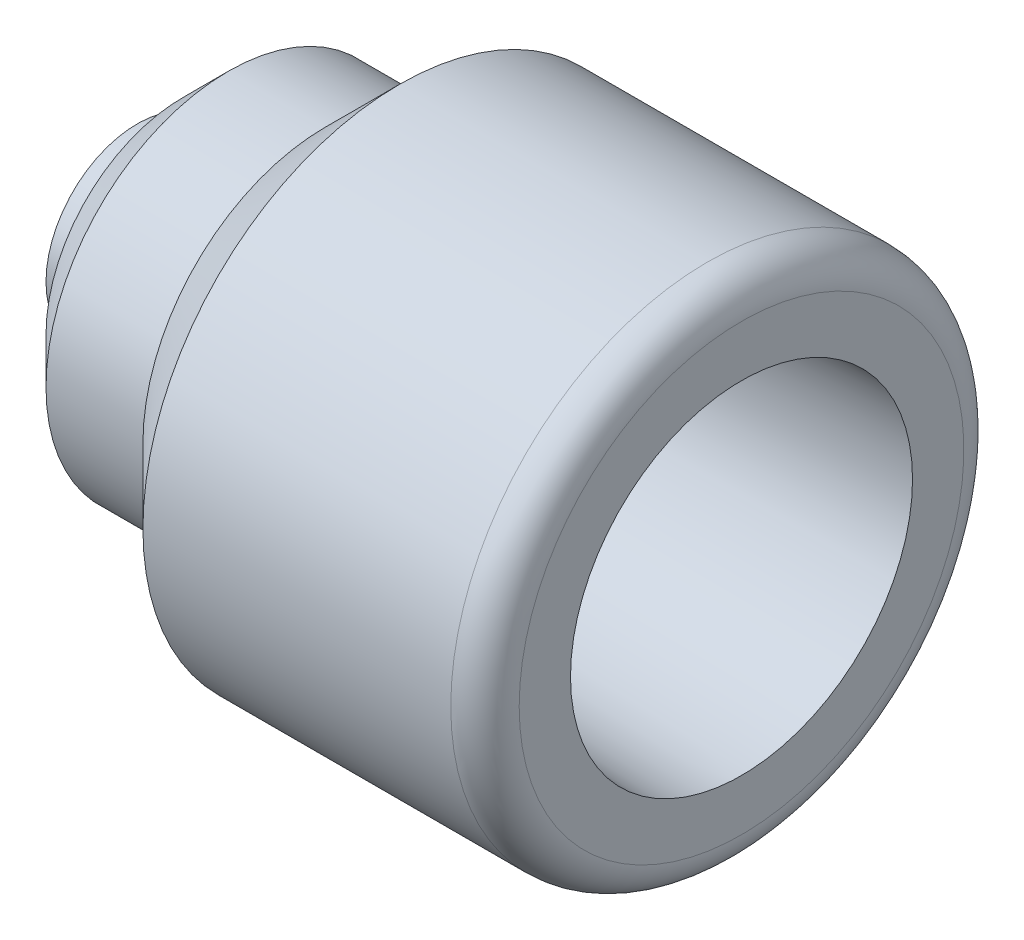
SolidWorks part; units mm, degrees
ref_plane "Plane1" through (0, 0, 0) normal (0, 0, 1) x (1, 0, 0)
ref_plane "Plane2" through (0, 0, 0) normal (0, 1, 0) x (1, 0, 0)
ref_plane "Plane3" through (0, 0, 0) normal (1, 0, 0) x (0, 0, -1)
sketch "Sketch1" plane through (0, 0, 0) normal (0, 0, 1) x (1, 0, 0)
  line L0 (0, 0) -> (80.4003, 0) construction
  line L1 (0, 8) -> (4, 8)
  line L2 (16.5, 16) -> (8, 16)
  line L3 (53, 15) -> (53, 19.5)
  line L4 (50, 22.5) -> (23, 22.5)
  line L5 (4, 8) -> (4, 12)
  line L6 (8, 16) -> (4, 12)
  line L7 (0, 8) -> (0, 5.1)
  line L8 (25, 13.2497) -> (25, 5.1)
  line L9 (25.7721, 14.0492) -> (53, 15)
  line L10 (0, 5.1) -> (25, 5.1)
  line L11 (16.5, 16) -> (23, 22.5)
  arc A0 (53, 19.5) -> (50, 22.5) centre (50, 19.5) ccw
  arc A1 (25, 13.2497) -> (25.7721, 14.0492) centre (25.8, 13.2497) cw
  dimension "D11" = 3
  dimension "D19" = 0.8
  dimension "D2" = 4
  dimension "D3" = 32
  dimension "D4" = 45
  dimension "D5" = 28
  dimension "D6" = 30
  dimension "D7" = 53
  dimension "D8" = 2
  dimension "D9" = 45
  dimension "D10" = 10.2
  dimension "D12" = 16
  dimension "D13" = 30
  dimension "D14" = 45
  dimension "D15" = 4
  dimension "D17" = 24
revolve "Revolve1" add sketch "Sketch1" angle 360 about L0
cosmetic thread "Cosmetic Thread1" parameters "D2"=12
